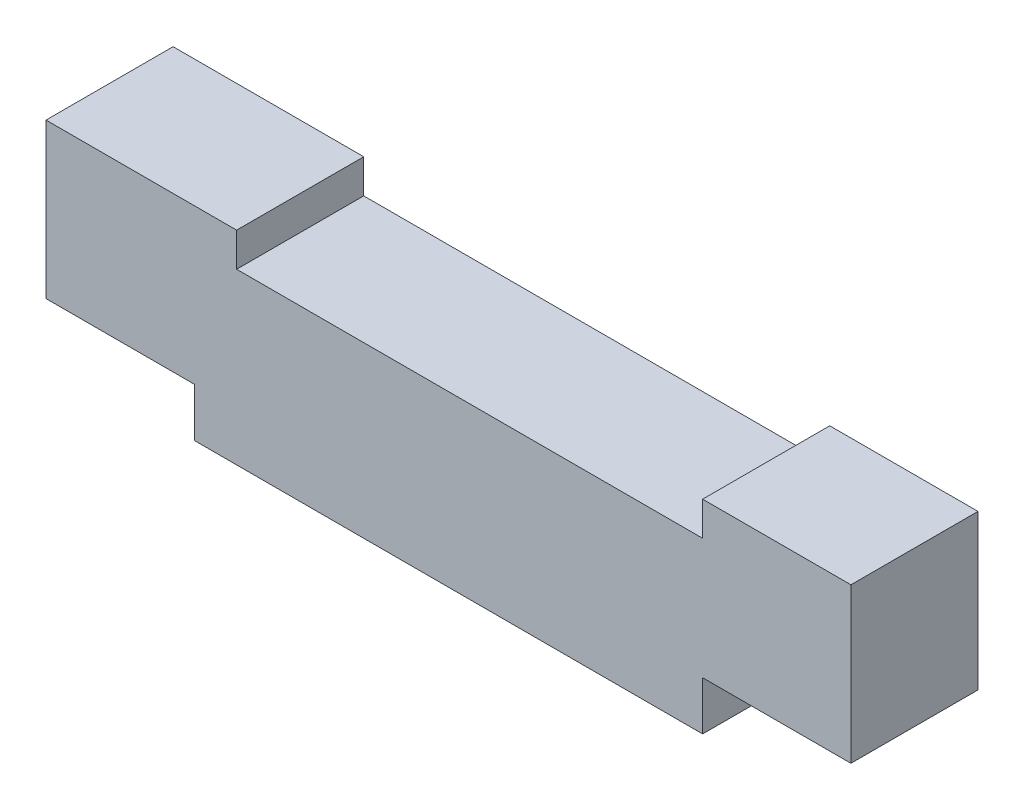
SolidWorks part; units mm, degrees
ref_plane "Plan de face" through (0, 0, 0) normal (0, 0, 1) x (1, 0, 0)
ref_plane "Plan de dessus" through (0, 0, 0) normal (0, 1, 0) x (1, 0, 0)
ref_plane "Plan de droite" through (0, 0, 0) normal (1, 0, 0) x (0, 0, -1)
sketch "Esquisse1" plane through (0, 0, 0) normal (0, 0, 1) x (1, 0, 0)
  line L0 (90, 0) -> (-30, 0)
  line L1 (-30, 0) -> (-30, 11.5)
  line L2 (30, 0) -> (30, 15) construction
  line L3 (90, 40) -> (-20, 40)
  line L4 (-20, 40) -> (-20, 48)
  line L5 (90, 11.5) -> (125, 11.5)
  line L6 (-65, 11.5) -> (-65, 48)
  line L7 (-65, 48) -> (-20, 48)
  line L9 (125, 11.5) -> (125, 48)
  line L10 (90, 0) -> (90, 11.5)
  line L11 (90, 40) -> (90, 48)
  line L12 (90, 48) -> (125, 48)
  line L14 (-30, 11.5) -> (-65, 11.5)
extrude "Extrusion1" add sketch "Esquisse1" along normal blind 30
